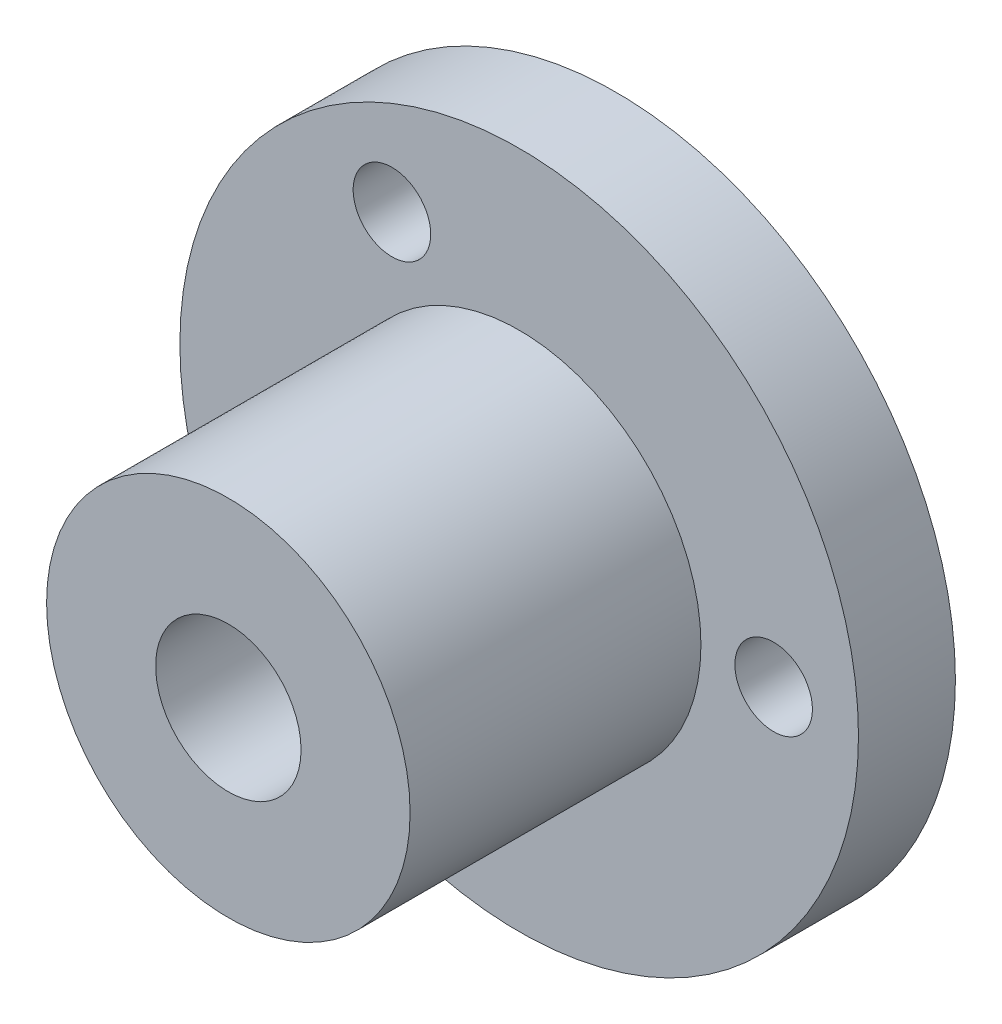
SolidWorks part; units mm, degrees
ref_plane "正面" through (0, 0, 0) normal (0, 0, 1) x (1, 0, 0)
ref_plane "平面" through (0, 0, 0) normal (0, 1, 0) x (1, 0, 0)
ref_plane "右側面" through (0, 0, 0) normal (1, 0, 0) x (0, 0, -1)
sketch "ｽｹｯﾁ1" plane through (0, 0, 0) normal (0, 0, 1) x (1, 0, 0)
  line L0 (0, 0) -> (10.5, 0)
  line L1 (0, 0) -> (-5.25, 9.0933)
  line L2 (0, 0) -> (-5.25, -9.0933)
  circle A0 centre (0, 0) radius 14
  circle A1 centre (10.5, 0) radius 1.6
  circle A2 centre (-5.25, 9.0933) radius 1.6
  circle A3 centre (-5.25, -9.0933) radius 1.6
  circle A4 centre (0, 0) radius 3
  dimension "D1" = 120
  dimension "D3" = 10.5
  dimension "D2" = 120
extrude "ﾎﾞｽ - 押し出し2" add sketch "ｽｹｯﾁ1" along normal blind 4
sketch "ｽｹｯﾁ2" plane through (0, 0, 4) normal (0, 0, 1) x (1, 0, 0)
  circle A0 centre (0, 0) radius 7.5
  circle A1 centre (0, 0) radius 3
extrude "ﾎﾞｽ - 押し出し3" add sketch "ｽｹｯﾁ2" along normal blind 12
